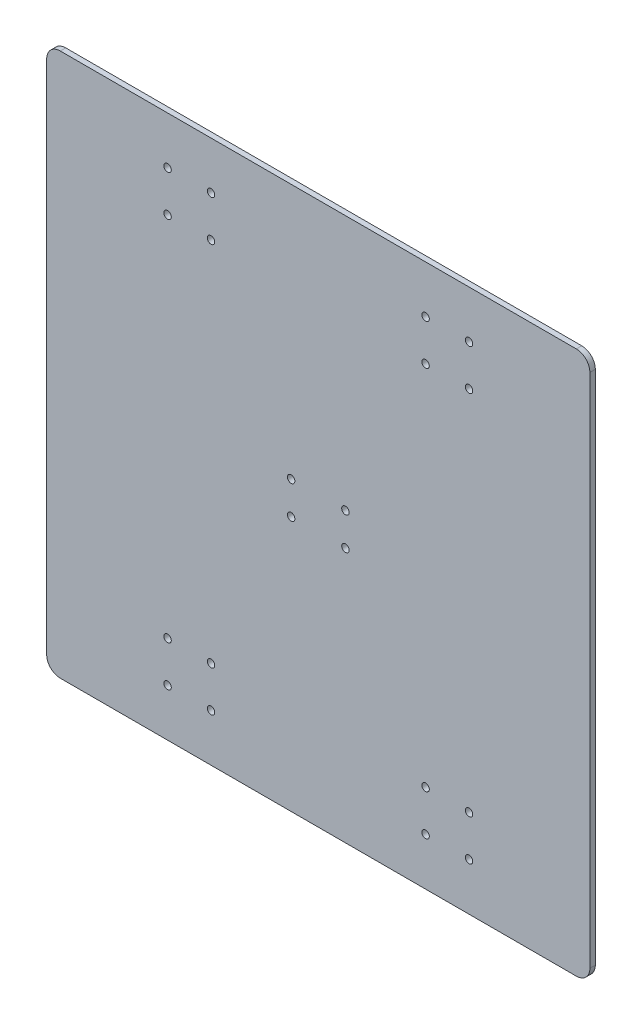
SolidWorks part; units mm, degrees
ref_plane "Спереди" through (0, 0, 0) normal (0, 0, 1) x (1, 0, 0)
ref_plane "Сверху" through (0, 0, 0) normal (0, 1, 0) x (1, 0, 0)
ref_plane "Справа" through (0, 0, 0) normal (1, 0, 0) x (0, 0, -1)
sketch "Эскиз1" plane through (0, 0, 0) normal (0, 0, 1) x (1, 0, 0)
  line L1 (-200, -200) -> (200, -200)
  line L2 (-200, -200) -> (-200, 200)
  line L3 (-200, 200) -> (200, 200)
  line L4 (200, -200) -> (200, 200)
  line L5 (-200, -200) -> (200, 200) construction
  line L6 (-200, 200) -> (200, -200) construction
  point P0 (0, 0)
  dimension "D1" = 400
  dimension "D2" = 400
extrude "Бобышка-Вытянуть1" add sketch "Эскиз1" along normal blind 4
hole_wizard "Диаметр отверстия Ø5.5 (5.5)1" positions "Эскиз4" profile "Эскиз5" hole size "Ø5.5" standard "DIN" end condition through all
sketch "Эскиз4" plane through (0, 0, 4) normal (0, 0, 1) x (1, 0, 0)
  line L1 (79, 135) -> (111, 165) construction
  line L3 (79, 165) -> (95, 150) construction
  point P0 (79, 165)
  point P2 (79, 135)
  point P4 (111, 135)
  point P6 (111, 165)
  point P24 (0, 0)
  dimension "D1" = 32
  dimension "D2" = 30
  dimension "D3" = 95
  dimension "D4" = 150
sketch "Эскиз5" plane through (79, 165, 4) normal (1, 0, 0) x (0, -1, 0)
  line L0 (0, 0) -> (0, 4)
  line L1 (0, 4) -> (2.75, 4)
  line L2 (2.75, 4) -> (2.75, 0)
  line L5 (2.75, 0) -> (0, 0)
  line L11 (0, -6.35) -> (0, 107.95) construction
  dimension "Диаметр сквозного отверстия" = 5.5
  dimension "Глубина сквозного отверстия" = 4
pattern_linear "Линейный массив1" count 2 spacing 300 along (0, -1, 0) count 2 spacing 190 along (-1, 0, 0) of "Диаметр отверстия Ø5.5 (5.5)1"
hole_wizard "Диаметр отверстия Ø5.5 (5.5)2" positions "Эскиз6" profile "Эскиз7" hole size "Ø5.5" standard "DIN" end condition through all
sketch "Эскиз6" plane through (0, 0, 4) normal (0, 0, 1) x (1, 0, 0)
  point P0 (20, 12)
  point P2 (-20, 12)
  point P4 (-20, -12)
  point P6 (20, -12)
  point P10 (0, 0)
  point P11 (0, 0)
  point P12 (0, 0)
  point P13 (0, 0)
  dimension "D1" = 24
  dimension "D2" = 40
  dimension "D3" = 20
  dimension "D4" = 12
sketch "Эскиз7" plane through (20, 12, 4) normal (1, 0, 0) x (0, -1, 0)
  line L0 (0, 0) -> (0, 4)
  line L1 (0, 4) -> (2.75, 4)
  line L2 (2.75, 4) -> (2.75, 0)
  line L5 (2.75, 0) -> (0, 0)
  line L11 (0, -6.35) -> (0, 107.95) construction
  dimension "Диаметр сквозного отверстия" = 5.5
  dimension "Глубина сквозного отверстия" = 4
fillet "Скругление1" radius 10 4 edges at (200, -200, 2) (-200, -200, 2) (-200, 200, 2) (200, 200, 2)
